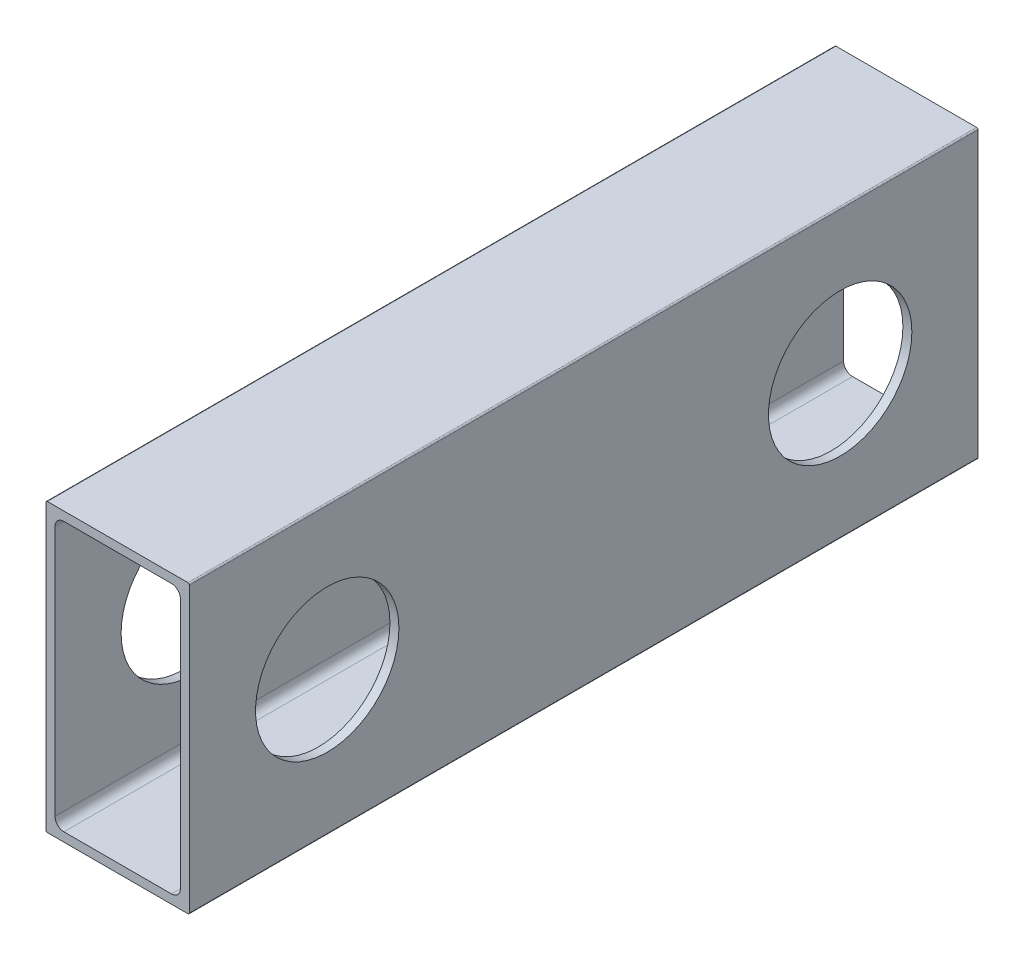
SolidWorks part; units mm, degrees
material "6061 Alloy"
ref_plane "Front Plane" through (0, 0, 0) normal (0, 0, 1) x (1, 0, 0)
ref_plane "Top Plane" through (0, 0, 0) normal (0, 1, 0) x (1, 0, 0)
ref_plane "Right Plane" through (0, 0, 0) normal (1, 0, 0) x (0, 0, -1)
ref_plane "Plane1" through (0, 0, 0) normal (0, 0, -1) x (-1, 0, 0)
sketch "Sketch1" plane through (0, 0, 0) normal (0, 0, -1) x (-1, 0, 0)
  line L0 (-11.1125, -22.225) -> (-11.1125, 22.225)
  line L1 (-9.525, 23.8125) -> (9.525, 23.8125)
  line L2 (11.1125, 22.225) -> (11.1125, -22.225)
  line L3 (9.525, -23.8125) -> (-9.525, -23.8125)
  line L4 (-12.7, 25.146) -> (-12.7, -25.146)
  line L5 (-12.446, -25.4) -> (12.446, -25.4)
  line L6 (12.7, -25.146) -> (12.7, 25.146)
  line L7 (12.446, 25.4) -> (-12.446, 25.4)
  arc A0 (-11.1125, 22.225) -> (-9.525, 23.8125) centre (-9.525, 22.225) cw
  arc A1 (9.525, 23.8125) -> (11.1125, 22.225) centre (9.525, 22.225) cw
  arc A2 (11.1125, -22.225) -> (9.525, -23.8125) centre (9.525, -22.225) cw
  arc A3 (-9.525, -23.8125) -> (-11.1125, -22.225) centre (-9.525, -22.225) cw
  arc A4 (-12.7, -25.146) -> (-12.446, -25.4) centre (-12.446, -25.146) ccw
  arc A5 (12.446, -25.4) -> (12.7, -25.146) centre (12.446, -25.146) ccw
  arc A6 (12.7, 25.146) -> (12.446, 25.4) centre (12.446, 25.146) ccw
  arc A7 (-12.446, 25.4) -> (-12.7, 25.146) centre (-12.446, 25.146) ccw
extrude "Boss-Extrude1" add sketch "Sketch1" against normal blind 139.7
sketch "Sketch2" plane through (12.7, 0, 0) normal (1, 0, 0) x (0, 0, -1)
  line L0 (-139.7, 25.146) -> (-139.7, -25.146) construction
  line L1 (0, 25.146) -> (0, -25.146) construction
  line L2 (-139.7, -25.4) -> (0, -25.4) construction
  circle A0 centre (-115.2825, 0) radius 12.7
  circle A1 centre (-24.4175, 0) radius 12.7
  dimension "D1" = 24.4175
  dimension "D2" = 24.4175
  dimension "D3" = 25.4
  dimension "D4" = 25.4
  dimension "D5" = 25.4
  dimension "D6" = 25.4
extrude "Cut-Extrude2" cut sketch "Sketch2" against normal through all
